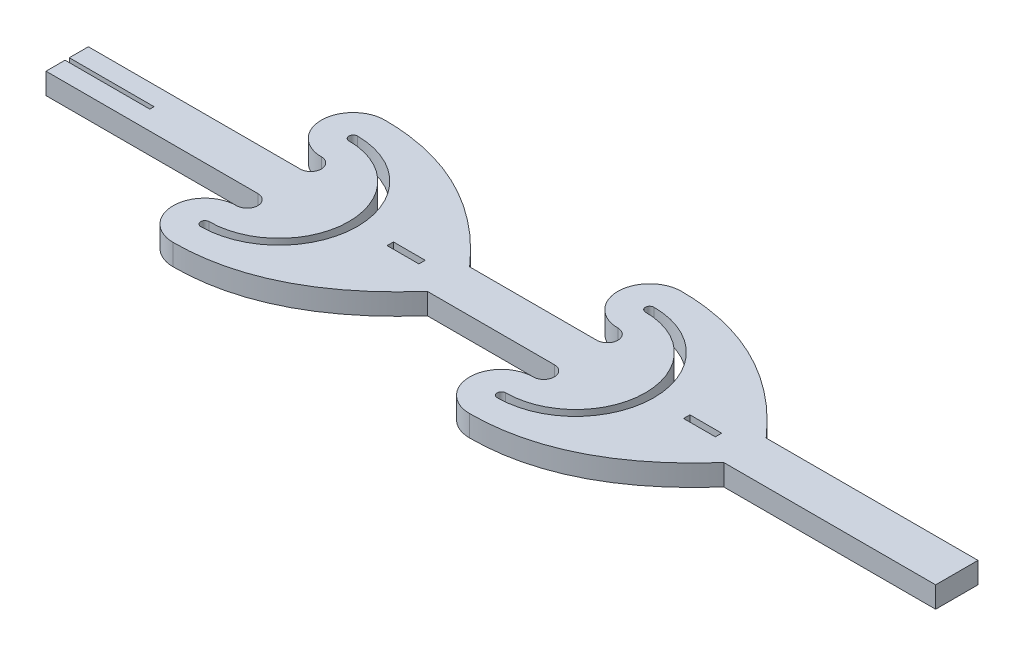
SolidWorks part; units mm, degrees
ref_plane "Front Plane" through (0, 0, 0) normal (0, 0, 1) x (1, 0, 0)
ref_plane "Top Plane" through (0, 0, 0) normal (0, 1, 0) x (1, 0, 0)
ref_plane "Right Plane" through (0, 0, 0) normal (1, 0, 0) x (0, 0, -1)
sketch "Sketch1" plane through (0, 0, 0) normal (0, 1, 0) x (1, 0, 0)
  line L1 (0, 1) -> (10, 1)
  line L3 (0, -1) -> (10, -1)
  line L5 (0, 1) -> (10, -1) construction
  line L6 (0, -1) -> (10, 1) construction
  line L13 (0, -0.1) -> (4, -0.1)
  line L14 (0, 0.1) -> (4, 0.1)
  line L15 (4, 0.1) -> (4, -0.1)
  line L16 (0, 0.1) -> (0, 1)
  line L17 (0, -0.1) -> (0, -1)
  line L19 (24, -1) -> (18, -1)
  line L22 (42, 1) -> (42, -1)
  line L23 (42, -1) -> (32, -1)
  line L24 (24, 1) -> (18, 1)
  line L25 (42, 1) -> (32, 1)
  arc A9 (10, 1) -> (10, 2) centre (10, 1.5) ccw
  arc A10 (10, 2) -> (10, 5) centre (10, 3.5) cw
  arc A11 (10, -2) -> (10, -5) centre (10, -3.5) ccw
  arc A12 (10, -1) -> (10, -2) centre (10, -1.5) cw
  arc A13 (24, 1) -> (24, 2) centre (24, 1.5) ccw
  arc A14 (24, 2) -> (24, 5) centre (24, 3.5) cw
  arc A15 (24, -2) -> (24, -5) centre (24, -3.5) ccw
  arc A16 (24, -1) -> (24, -2) centre (24, -1.5) cw
  spline S0 degree 2 poles (10, -5) (14.4756, -4.9982) (18, -1) knots 0 0 0 1 1 1
  spline S1 degree 2 poles (24, -5) (28.4756, -4.9982) (32, -1) knots 0 0 0 1 1 1
  spline S2 degree 2 poles (10, 5) (14.4756, 4.9982) (18, 1) knots 0 0 0 1 1 1
  spline S3 degree 2 poles (24, 5) (28.4756, 4.9982) (32, 1) knots 0 0 0 1 1 1
  point P4 (5, 0)
  point P19 (16, 0)
  point P40 (30, 0)
  dimension "D1" = 1.5
  dimension "D2" = 6
  dimension "D6" = 1.5
  dimension "D7" = 1.5
  dimension "D8" = 1.5
  dimension "D3" = 10
  dimension "D5" = 10
  dimension "D4" = 6
extrude "Boss-Extrude1" add sketch "Sketch1" along normal blind 1
sketch "Sketch2" plane through (0, 1, 0) normal (0, 1, 0) x (1, 0, 0)
  line L1 (15.1829, -0.0789) -> (16.6829, -0.0789)
  line L2 (15.1829, -0.0789) -> (15.1829, 0.2211)
  line L3 (15.1829, 0.2211) -> (16.6829, 0.2211)
  line L4 (16.6829, -0.0789) -> (16.6829, 0.2211)
  line L5 (15.1829, -0.0789) -> (16.6829, 0.2211) construction
  line L6 (15.1829, 0.2211) -> (16.6829, -0.0789) construction
  line L7 (29.25, -0.15) -> (30.75, -0.15)
  line L8 (29.25, -0.15) -> (29.25, 0.15)
  line L9 (29.25, 0.15) -> (30.75, 0.15)
  line L10 (30.75, -0.15) -> (30.75, 0.15)
  line L11 (29.25, -0.15) -> (30.75, 0.15) construction
  line L12 (29.25, 0.15) -> (30.75, -0.15) construction
  arc A0 (10, -3.7) -> (10, 3.7) centre (10, 0) ccw
  arc A13 (10, 3.3) -> (10, 3.7) centre (10, 3.5) cw
  arc A14 (10, -3.3) -> (10, 3.3) centre (10, 0) ccw
  arc A15 (10, -3.3) -> (10, -3.7) centre (10, -3.5) ccw
  arc A20 (24, -3.7) -> (24, 3.7) centre (24, 0) ccw
  arc A21 (24, 3.3) -> (24, 3.7) centre (24, 3.5) cw
  arc A22 (24, -3.3) -> (24, 3.3) centre (24, 0) ccw
  arc A23 (24, -3.3) -> (24, -3.7) centre (24, -3.5) ccw
  point P0 (15.9329, 0.0711)
  point P4 (15.9329, 0.0711)
  point P13 (30, 0)
  point P16 (30, 0)
extrude "Cut-Extrude1" cut sketch "Sketch2" against normal blind 1
